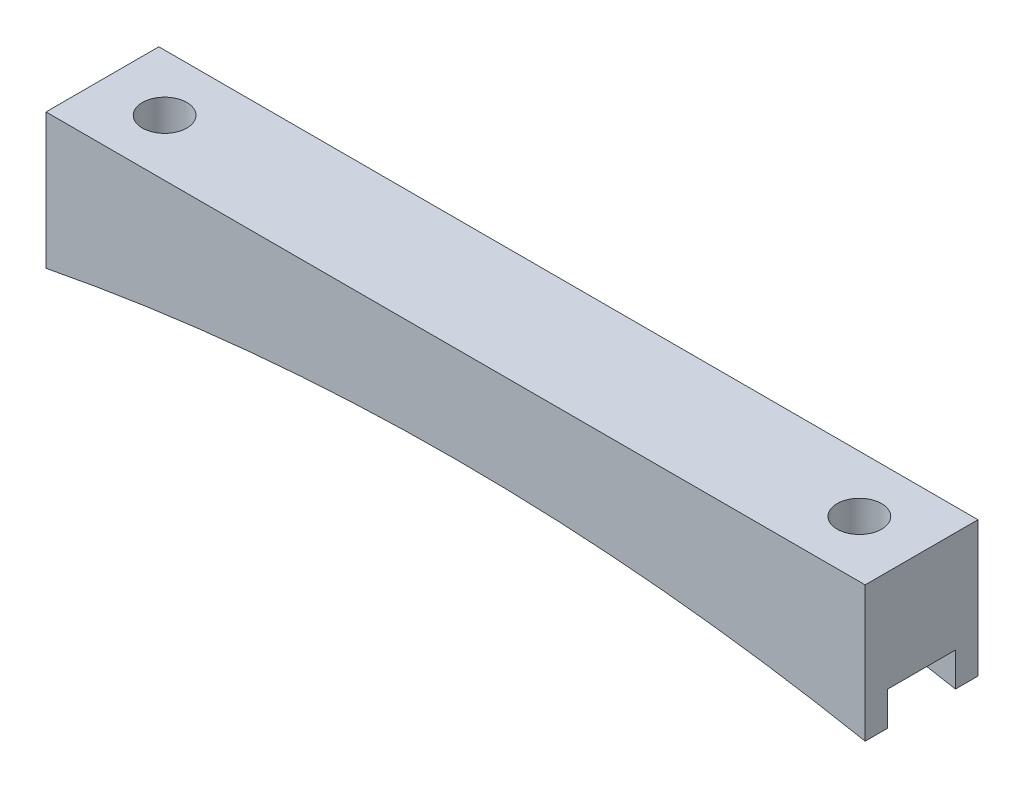
SolidWorks part; units mm, degrees
ref_plane "Front Plane" through (0, 0, 0) normal (0, 0, 1) x (1, 0, 0)
ref_plane "Top Plane" through (0, 0, 0) normal (0, 1, 0) x (1, 0, 0)
ref_plane "Right Plane" through (0, 0, 0) normal (1, 0, 0) x (0, 0, -1)
sketch "Sketch1" plane through (0, 0, 0) normal (0, 0, 1) x (1, 0, 0)
  line L0 (-46.095, 0) -> (46.095, 0)
  line L1 (-39.095, -2.54) -> (39.095, -2.54) construction
  line L2 (0, 0) -> (0, -4.6068) construction
  line L3 (46.095, 0) -> (46.095, -15.24)
  line L4 (-46.095, 0) -> (-46.095, -15.24)
  arc A0 (-46.095, -15.24) -> (46.095, -15.24) centre (0, -252.0964) cw
  point P4 (0, 0)
  point P9 (0, -2.54)
  dimension "D4" = 241.3
  dimension "D1" = 78.19
  dimension "D2" = 2.54
  dimension "D3" = 7
  dimension "D5" = 15.24
extrude "Boss-Extrude1" add sketch "Sketch1" along normal blind 12.7
sketch "Sketch2" plane through (0, 0, 0) normal (0, 1, 0) x (1, 0, 0)
  line L1 (-39.095, 0) -> (-39.095, -12.7) construction
  line L2 (-46.095, 0) -> (46.095, 0) construction
  line L3 (46.095, -12.7) -> (-46.095, -12.7) construction
  line L4 (39.095, 0) -> (39.095, -12.7) construction
  circle A0 centre (-39.095, -6.35) radius 2.5
  circle A1 centre (39.095, -6.35) radius 2.5
  circle A2 centre (-39.095, -6.35) radius 3 construction
  point P7 (-39.095, -6.35)
  dimension "D1" = 5
  dimension "D2" = 6
extrude "Cut-Extrude1" cut sketch "Sketch2" against normal through all
sketch "Sketch3" plane through (46.095, 0, 0) normal (1, 0, 0) x (0, 0, -1)
  line L0 (-12.7, -15.24) -> (0, -15.24) construction
  line L1 (-10.16, -15.24) -> (-2.54, -15.24)
  line L2 (-10.16, -15.24) -> (-10.16, -11.43)
  line L3 (-10.16, -11.43) -> (-2.54, -11.43)
  line L4 (-2.54, -15.24) -> (-2.54, -11.43)
  line L5 (-12.7, -15.24) -> (-12.7, 0) construction
  line L6 (0, -15.24) -> (0, 0) construction
  dimension "D1" = 2.54
  dimension "D2" = 2.54
  dimension "D3" = 3.81
extrude "Cut-Extrude2" cut sketch "Sketch3" against normal through all
